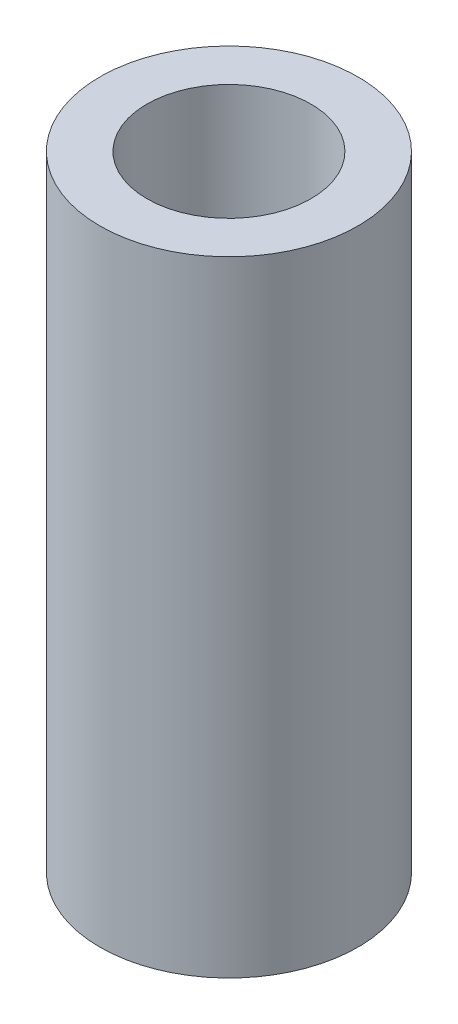
SolidWorks part; units mm, degrees
ref_plane "Front Plane" through (0, 0, 0) normal (0, 0, 1) x (1, 0, 0)
ref_plane "Top Plane" through (0, 0, 0) normal (0, 1, 0) x (1, 0, 0)
ref_plane "Right Plane" through (0, 0, 0) normal (1, 0, 0) x (0, 0, -1)
sketch "Sketch1" plane through (0, 0, 0) normal (0, 1, 0) x (1, 0, 0)
  circle A0 centre (0, 0) radius 2.5019
  circle A1 centre (0, 0) radius 3.937
  dimension "D1" = 5.0038
  dimension "D2" = 7.874
extrude "Boss-Extrude1" add sketch "Sketch1" along normal blind 19.05
